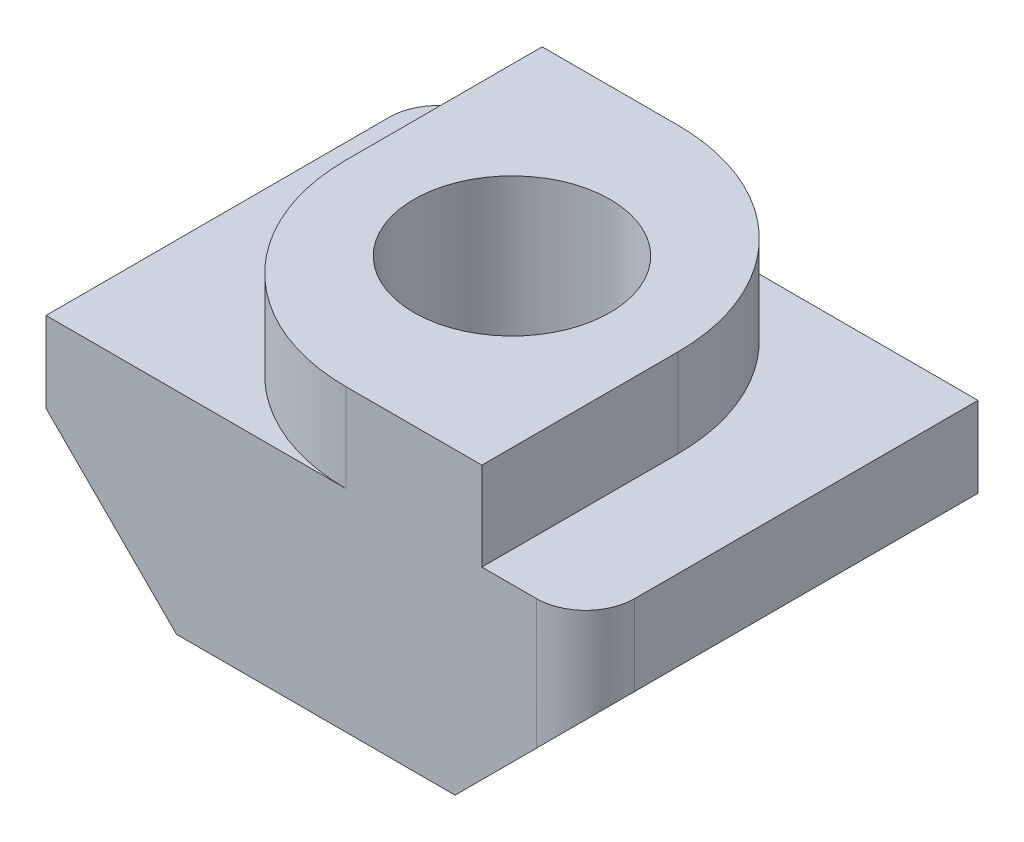
SolidWorks part; units mm, degrees
ref_plane "Front" through (0, 0, 0) normal (0, 0, 1) x (1, 0, 0)
ref_plane "Top" through (0, 0, 0) normal (0, 1, 0) x (1, 0, 0)
ref_plane "Right" through (0, 0, 0) normal (1, 0, 0) x (0, 0, -1)
sketch "Sketch1" plane through (0, 0, 0) normal (0, 1, 0) x (1, 0, 0)
  line L1 (-5.5, -4) -> (5.5, -4)
  line L2 (-5.5, -4) -> (-5.5, 4)
  line L3 (-5.5, 4) -> (5.5, 4)
  line L4 (5.5, -4) -> (5.5, 4)
  line L5 (-5.5, -4) -> (5.5, 4) construction
  line L6 (-5.5, 4) -> (5.5, -4) construction
  circle A0 centre (0, 0) radius 2
  point P0 (0, 0)
  dimension "D1" = 4
  dimension "D2" = 11
  dimension "D3" = 8
extrude "Boss-Extrude1" add sketch "Sketch1" along normal blind 4.3
sketch "Sketch2" plane through (0, 0, 4) normal (0, 0, 1) x (1, 0, 0)
  line L0 (-5.5, 2.66) -> (-2.84, 0)
  line L1 (-5.5, 4.3) -> (-5.5, 0) construction
  line L2 (-5.5, 0) -> (5.5, 0) construction
  line L3 (-5.5, 2.66) -> (-5.5, 0)
  line L4 (-5.5, 0) -> (-2.84, 0)
  line L5 (0, 0) -> (0, 4.3) construction
  line L6 (-5.5, 4.3) -> (5.5, 4.3) construction
  line L7 (5.5, 2.66) -> (5.5, 0)
  line L8 (5.5, 0) -> (2.84, 0)
  line L9 (5.5, 2.66) -> (2.84, 0)
  dimension "D1" = 1.64
  dimension "D2" = 45
extrude "Cut-Extrude1" cut sketch "Sketch2" against normal through all
sketch "Sketch3" plane through (0, 4.3, 0) normal (0, 1, 0) x (1, 0, 0)
  line L0 (5.5, 4) -> (-5.5, 4) construction
  line L1 (-3.385, -4) -> (3.385, -4)
  line L2 (-3.385, -4) -> (-3.385, 4)
  line L3 (-3.385, 4) -> (3.385, 4)
  line L4 (3.385, -4) -> (3.385, 4)
  line L5 (-3.385, -4) -> (3.385, 4) construction
  line L6 (-3.385, 4) -> (3.385, -4) construction
  circle A0 centre (0, 0) radius 2
  point P0 (0, 0)
  dimension "D2" = 4
  dimension "D1" = 6.77
extrude "Boss-Extrude2" add sketch "Sketch3" along normal blind 1.8
fillet "Fillet1" radius 4 2 edges
fillet "Fillet2" radius 1 2 edges at (5.5, 3.48, 4) (-5.5, 3.48, -4)
